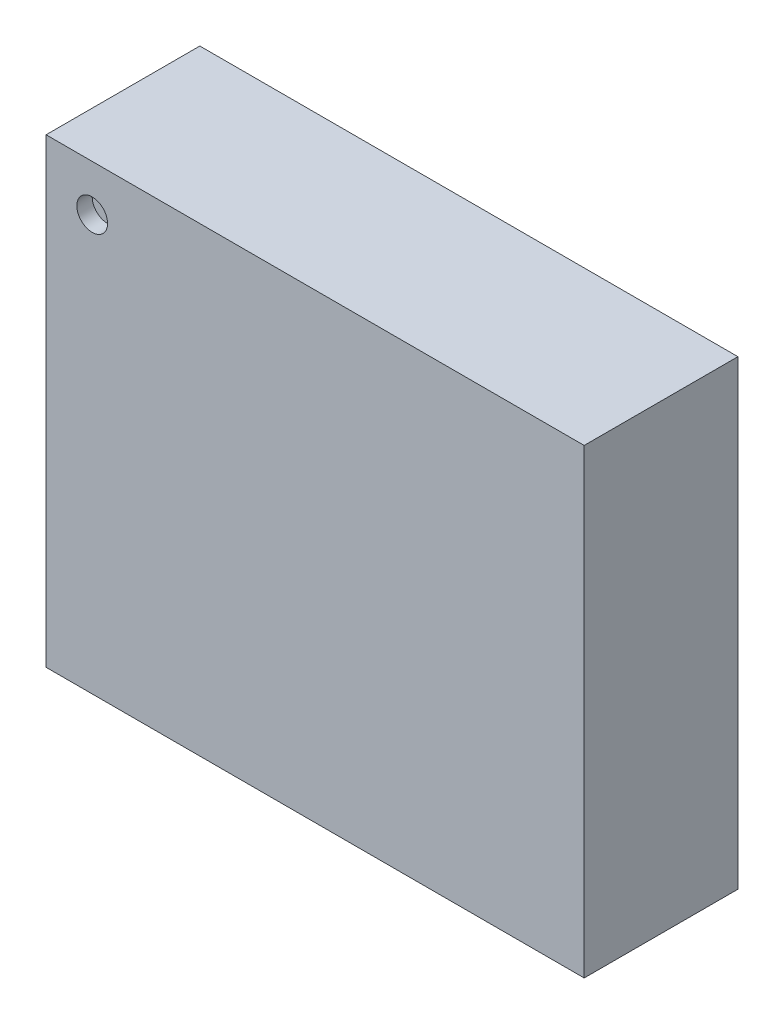
SolidWorks part; units mm, degrees
ref_plane "Front Plane" through (0, 0, 0) normal (0, 0, 1) x (1, 0, 0)
ref_plane "Top Plane" through (0, 0, 0) normal (0, 1, 0) x (1, 0, 0)
ref_plane "Right Plane" through (0, 0, 0) normal (1, 0, 0) x (0, 0, -1)
sketch "Sketch1" plane through (0, 0, 0) normal (0, 0, 1) x (1, 0, 0)
  line L1 (0, 0) -> (3.5, 0)
  line L2 (0, 0) -> (0, 3)
  line L3 (0, 3) -> (3.5, 3)
  line L4 (3.5, 0) -> (3.5, 3)
  dimension "D1" = 3.5
  dimension "D2" = 3
extrude "Boss-Extrude1" add sketch "Sketch1" along normal blind 1
sketch "Sketch2" plane through (0, 0, 1) normal (0, 0, 1) x (1, 0, 0)
  line L0 (3.5, 3) -> (0, 3) construction
  line L1 (0, 3) -> (0, 0) construction
  circle A0 centre (0.3, 2.7) radius 0.1
  dimension "D3" = 0.2
  dimension "D1" = 0.3
  dimension "D2" = 0.3
extrude "Cut-Extrude1" cut sketch "Sketch2" against normal blind 0.1
sketch "Sketch3" plane through (0, 0, 0) normal (0, 0, -1) x (-1, 0, 0)
  line L0 (-1.75, 3) -> (-1.75, 0) construction
  line L1 (-3.5, 3) -> (0, 3) construction
  line L2 (0, 0) -> (-3.5, 0) construction
  line L3 (-3.255, 2.9) -> (-3.255, 2.55) construction
  line L4 (0, 3) -> (0, 0) construction
  line L5 (0, 1.5) -> (-3.5, 1.5) construction
  line L6 (-3.5, 0) -> (-3.5, 3) construction
  line L7 (-3.37, 2.9) -> (-3.14, 2.9)
  line L8 (-3.37, 2.9) -> (-3.37, 2.55)
  line L9 (-3.37, 2.55) -> (-3.14, 2.55)
  line L10 (-3.14, 2.9) -> (-3.14, 2.55)
  line L11 (-2.94, 2.9) -> (-2.71, 2.9)
  line L12 (-2.94, 2.9) -> (-2.94, 2.55)
  line L13 (-2.94, 2.55) -> (-2.71, 2.55)
  line L14 (-2.71, 2.9) -> (-2.71, 2.55)
  line L15 (-2.51, 2.9) -> (-2.28, 2.9)
  line L16 (-2.51, 2.9) -> (-2.51, 2.55)
  line L17 (-2.51, 2.55) -> (-2.28, 2.55)
  line L18 (-2.28, 2.9) -> (-2.28, 2.55)
  line L19 (-2.08, 2.9) -> (-1.85, 2.9)
  line L20 (-2.08, 2.9) -> (-2.08, 2.55)
  line L21 (-2.08, 2.55) -> (-1.85, 2.55)
  line L22 (-1.85, 2.9) -> (-1.85, 2.55)
  line L23 (-1.65, 2.9) -> (-1.42, 2.9)
  line L24 (-1.65, 2.9) -> (-1.65, 2.55)
  line L25 (-1.65, 2.55) -> (-1.42, 2.55)
  line L26 (-1.42, 2.9) -> (-1.42, 2.55)
  line L27 (-1.22, 2.9) -> (-0.99, 2.9)
  line L28 (-1.22, 2.9) -> (-1.22, 2.55)
  line L29 (-1.22, 2.55) -> (-0.99, 2.55)
  line L30 (-0.99, 2.9) -> (-0.99, 2.55)
  line L31 (-0.79, 2.9) -> (-0.56, 2.9)
  line L32 (-0.79, 2.9) -> (-0.79, 2.55)
  line L33 (-0.79, 2.55) -> (-0.56, 2.55)
  line L34 (-0.56, 2.9) -> (-0.56, 2.55)
  line L35 (-0.36, 2.9) -> (-0.13, 2.9)
  line L36 (-0.36, 2.9) -> (-0.36, 2.55)
  line L37 (-0.36, 2.55) -> (-0.23, 2.55)
  line L38 (-0.13, 2.9) -> (-0.13, 2.65)
  line L39 (-0.13, 0.1) -> (-0.13, 0.45)
  line L40 (-0.36, 0.45) -> (-0.13, 0.45)
  line L41 (-0.36, 0.1) -> (-0.36, 0.45)
  line L42 (-0.36, 0.1) -> (-0.13, 0.1)
  line L43 (-0.56, 0.1) -> (-0.56, 0.45)
  line L44 (-0.79, 0.45) -> (-0.56, 0.45)
  line L45 (-0.79, 0.1) -> (-0.79, 0.45)
  line L46 (-0.79, 0.1) -> (-0.56, 0.1)
  line L47 (-0.99, 0.1) -> (-0.99, 0.45)
  line L48 (-1.22, 0.45) -> (-0.99, 0.45)
  line L49 (-1.22, 0.1) -> (-1.22, 0.45)
  line L50 (-1.22, 0.1) -> (-0.99, 0.1)
  line L51 (-1.42, 0.1) -> (-1.42, 0.45)
  line L52 (-1.65, 0.45) -> (-1.42, 0.45)
  line L53 (-1.65, 0.1) -> (-1.65, 0.45)
  line L54 (-1.65, 0.1) -> (-1.42, 0.1)
  line L55 (-1.85, 0.1) -> (-1.85, 0.45)
  line L56 (-2.08, 0.45) -> (-1.85, 0.45)
  line L57 (-2.08, 0.1) -> (-2.08, 0.45)
  line L58 (-2.08, 0.1) -> (-1.85, 0.1)
  line L59 (-2.28, 0.1) -> (-2.28, 0.45)
  line L60 (-2.51, 0.45) -> (-2.28, 0.45)
  line L61 (-2.51, 0.1) -> (-2.51, 0.45)
  line L62 (-2.51, 0.1) -> (-2.28, 0.1)
  line L63 (-2.71, 0.1) -> (-2.71, 0.45)
  line L64 (-2.94, 0.45) -> (-2.71, 0.45)
  line L65 (-2.94, 0.1) -> (-2.94, 0.45)
  line L66 (-2.94, 0.1) -> (-2.71, 0.1)
  line L67 (-3.14, 0.1) -> (-3.14, 0.45)
  line L68 (-3.37, 0.45) -> (-3.14, 0.45)
  line L69 (-3.37, 0.1) -> (-3.37, 0.45)
  line L70 (-3.37, 0.1) -> (-3.14, 0.1)
  line L71 (-3.05, 2.145) -> (-3.4, 2.145) construction
  line L72 (-3.4, 2.26) -> (-3.05, 2.26)
  line L73 (-3.4, 2.26) -> (-3.4, 2.03)
  line L74 (-3.4, 2.03) -> (-3.05, 2.03)
  line L75 (-3.05, 2.26) -> (-3.05, 2.03)
  line L76 (-3.4, 1.83) -> (-3.05, 1.83)
  line L77 (-3.4, 1.83) -> (-3.4, 1.6)
  line L78 (-3.4, 1.6) -> (-3.05, 1.6)
  line L79 (-3.05, 1.83) -> (-3.05, 1.6)
  line L80 (-3.4, 1.4) -> (-3.05, 1.4)
  line L81 (-3.4, 1.4) -> (-3.4, 1.17)
  line L82 (-3.4, 1.17) -> (-3.05, 1.17)
  line L83 (-3.05, 1.4) -> (-3.05, 1.17)
  line L84 (-3.4, 0.97) -> (-3.05, 0.97)
  line L85 (-3.4, 0.97) -> (-3.4, 0.74)
  line L86 (-3.4, 0.74) -> (-3.05, 0.74)
  line L87 (-3.05, 0.97) -> (-3.05, 0.74)
  line L88 (-0.45, 0.97) -> (-0.45, 0.74)
  line L89 (-0.1, 0.74) -> (-0.45, 0.74)
  line L90 (-0.1, 0.97) -> (-0.1, 0.74)
  line L91 (-0.1, 0.97) -> (-0.45, 0.97)
  line L92 (-0.45, 1.4) -> (-0.45, 1.17)
  line L93 (-0.1, 1.17) -> (-0.45, 1.17)
  line L94 (-0.1, 1.4) -> (-0.1, 1.17)
  line L95 (-0.1, 1.4) -> (-0.45, 1.4)
  line L96 (-0.45, 1.83) -> (-0.45, 1.6)
  line L97 (-0.1, 1.6) -> (-0.45, 1.6)
  line L98 (-0.1, 1.83) -> (-0.1, 1.6)
  line L99 (-0.1, 1.83) -> (-0.45, 1.83)
  line L100 (-0.45, 2.26) -> (-0.45, 2.03)
  line L101 (-0.1, 2.03) -> (-0.45, 2.03)
  line L102 (-0.1, 2.26) -> (-0.1, 2.03)
  line L103 (-0.1, 2.26) -> (-0.45, 2.26)
  line L104 (-0.23, 2.55) -> (-0.13, 2.65)
  point P6 (0, 1.5)
  point P13 (-1.75, 3)
  dimension "D1" = 0.35
  dimension "D2" = 0.23
  dimension "D3" = 0.1
  dimension "D4" = 1.505
  dimension "D6" = 0.35
  dimension "D7" = 0.23
  dimension "D8" = 0.1
  dimension "D9" = 0.645
  dimension "D11" = 135
  dimension "D12" = 0.25
  dimension "D5" = 8
  dimension "D10" = 4
extrude "Boss-Extrude2" add sketch "Sketch3" along normal blind 0.05
